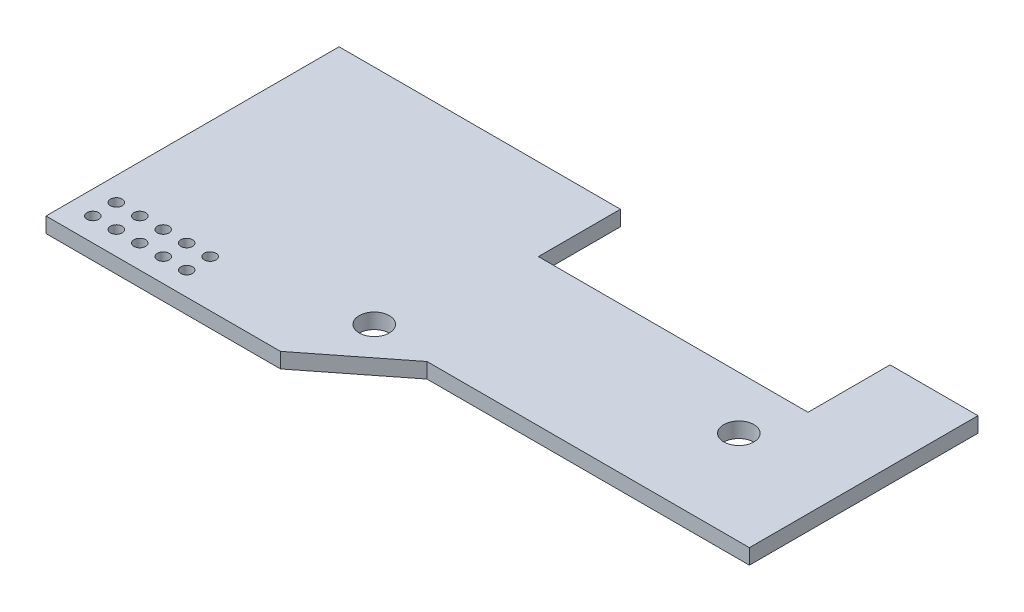
SolidWorks part; units mm, degrees
ref_plane "Front" through (0, 0, 0) normal (0, 0, 1) x (1, 0, 0)
ref_plane "Top" through (0, 0, 0) normal (0, 1, 0) x (1, 0, 0)
ref_plane "Right" through (0, 0, 0) normal (1, 0, 0) x (0, 0, -1)
sketch "Sketch1" plane through (0, 0, 0) normal (0, 1, 0) x (1, 0, 0)
  line L0 (45.085, -43.6134) -> (45.085, 21.5536) construction
  line L1 (0, 0) -> (30.48, 0)
  line L2 (0, 0) -> (0, -31.75)
  line L3 (45.085, -8.89) -> (59.69, -8.89)
  line L4 (30.48, 0) -> (30.48, -8.89)
  line L5 (0, -31.75) -> (25.4, -31.75)
  line L6 (34.29, -24.765) -> (25.4, -31.75)
  line L7 (34.29, -24.765) -> (45.085, -24.765)
  line L8 (45.085, -24.765) -> (45.085, -8.89) construction
  line L9 (45.085, -8.89) -> (30.48, -8.89)
  line L10 (59.69, -8.89) -> (59.69, 0)
  line L11 (59.69, 0) -> (69.215, 0)
  line L12 (69.215, 0) -> (69.215, -24.765)
  line L13 (69.215, -24.765) -> (45.085, -24.765)
  point P0 (0, 0)
  dimension "D2" = 9.525
  dimension "D1" = 30.48
  dimension "D3" = 25.4
  dimension "D4" = 8.89
  dimension "D5" = 31.75
  dimension "D6" = 15.875
  dimension "D7" = 34.29
extrude "Boss-Extrude1" add sketch "Sketch1" along normal blind 1.651
sketch "Sketch5" plane through (0, 1.651, 0) normal (0, 1, 0) x (1, 0, 0)
  line L0 (2.54, -26.67) -> (12.7, -29.21) construction
  line L1 (0, 0) -> (0, -31.75) construction
  line L2 (0, -31.75) -> (25.4, -31.75) construction
  circle A0 centre (2.54, -29.21) radius 0.635
  circle A1 centre (5.08, -29.21) radius 0.635
  circle A2 centre (7.62, -29.21) radius 0.635
  circle A3 centre (10.16, -29.21) radius 0.635
  circle A4 centre (12.7, -29.21) radius 0.635
  circle A5 centre (2.54, -26.67) radius 0.635
  circle A6 centre (5.08, -26.67) radius 0.635
  circle A7 centre (7.62, -26.67) radius 0.635
  circle A8 centre (10.16, -26.67) radius 0.635
  circle A9 centre (12.7, -26.67) radius 0.635
  point P2 (7.62, -27.94)
  dimension "D1" = 1.27
  dimension "D4" = 2.54
  dimension "D5" = 2.54
  dimension "D6" = 7.62
  dimension "D7" = 3.81
  dimension "D2" = 5
  dimension "D3" = 2
extrude "Cut-Extrude2" cut sketch "Sketch5" against normal through all
hole_wizard "#4 Clearance Hole1" positions "Sketch8" profile "Sketch7" hole size "#4" standard "Ansi Inch" end condition through all
sketch "Sketch8" plane through (0, 1.651, 0) normal (0, 1, 0) x (-1, 0, 0)
  line L0 (0, 0) -> (0, 31.75) construction
  line L1 (0, 31.75) -> (-25.4, 31.75) construction
  point P1 (-27.94, 24.13)
  point P2 (-57.912, 14.605)
  dimension "D1" = 27.94
  dimension "D2" = 7.62
  dimension "D3" = 57.912
  dimension "D4" = 17.145
sketch "Sketch7" plane through (27.94, 1.651, 24.13) normal (1, 0, 0) x (0, 0, 1)
  line L0 (0, 0) -> (0, 1.651)
  line L1 (0, 1.651) -> (1.6319, 1.651)
  line L2 (1.6319, 1.651) -> (1.6319, 0)
  line L5 (1.6319, 0) -> (0, 0)
  line L11 (0, -6.35) -> (0, 107.95) construction
  dimension "Thru Hole Dia." = 3.2639
  dimension "Thru Hole Depth" = 1.651
